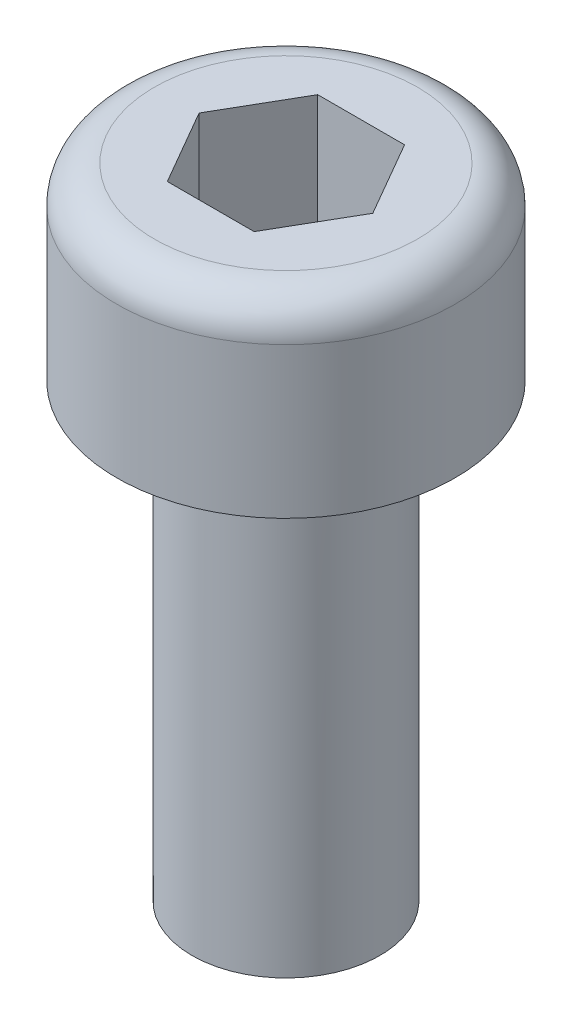
SolidWorks part; units mm, degrees
material "Alloy Steel"
ref_plane "Plane1" through (0, 0, 0) normal (0, 0, 1) x (1, 0, 0)
ref_plane "Plane2" through (0, 0, 0) normal (0, 1, 0) x (1, 0, 0)
ref_plane "Plane3" through (0, 0, 0) normal (1, 0, 0) x (0, 0, -1)
sketch "Sketch1" plane through (0, 0, 0) normal (0, 0, 1) x (1, 0, 0)
  line L0 (0, -6.3349) -> (0, 2.5)
  line L1 (0, 2.5) -> (1.75, 2.5)
  line L2 (2.25, 2) -> (2.25, 0)
  line L3 (2.25, 0) -> (1.25, 0)
  line L4 (1.25, 0) -> (1.25, -6)
  line L5 (1.25, -6) -> (0, -6.3349)
  line L6 (0, 2.5) -> (0, 17) construction
  arc A0 (1.75, 2.5) -> (2.25, 2) centre (1.75, 2) cw
  point P10 (2.25, 2.5)
  dimension "D6" = 0.5
  dimension "D1" = 4.5
  dimension "D2" = 2.5
  dimension "D3" = 2.5
  dimension "D4" = 6
  dimension "D5" = 75
revolve "Base-Revolve" add sketch "Sketch1" angle 360 about L6
sketch "Sketch2" plane through (0, 2.5, 0) normal (0, 1, 0) x (-1, 0, 0)
  line L1 (-1.1547, 0) -> (-0.5774, -1)
  line L2 (-0.5774, -1) -> (0.5774, -1)
  line L3 (0.5774, -1) -> (1.1547, 0)
  line L4 (1.1547, 0) -> (0.5774, 1)
  line L5 (0.5774, 1) -> (-0.5774, 1)
  line L6 (-0.5774, 1) -> (-1.1547, 0)
  circle A0 centre (0, 0) radius 1 construction
  dimension "D1" = 2
extrude "Cut-Extrude1" cut sketch "Sketch2" against normal blind 2
